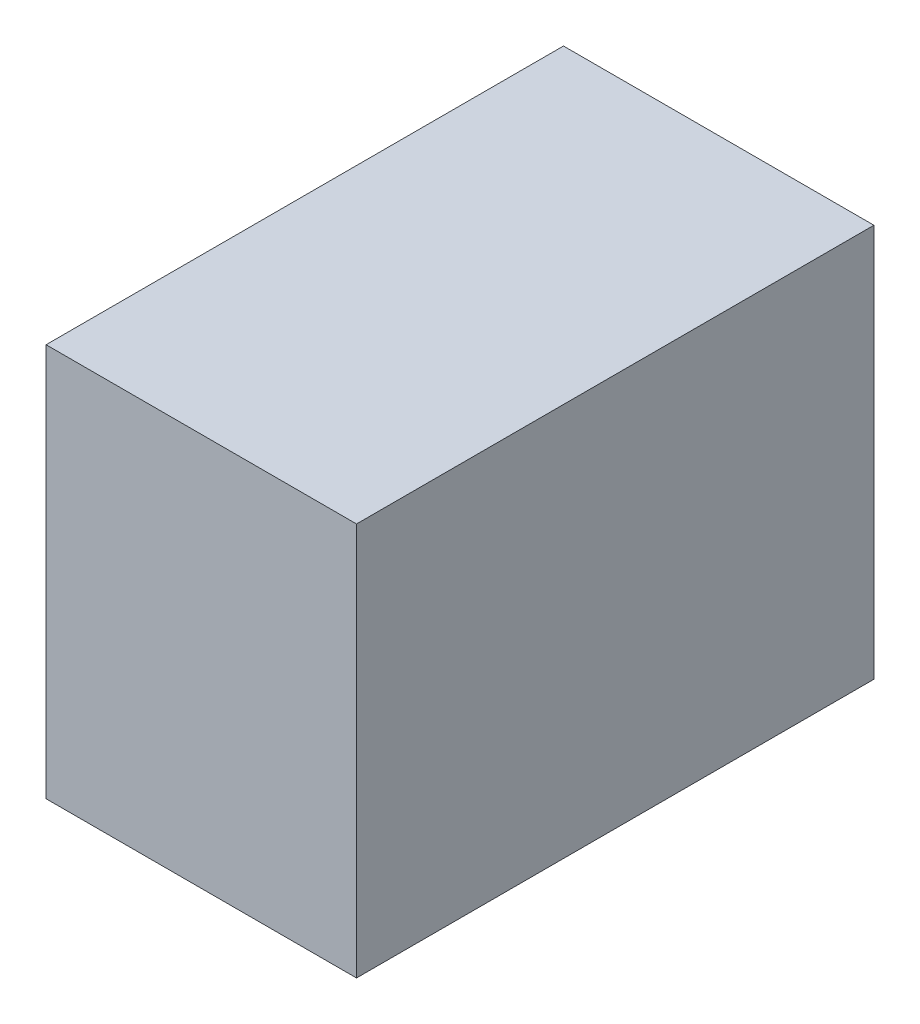
SolidWorks part; units mm, degrees
ref_plane "Front Plane" through (0, 0, 0) normal (0, 0, 1) x (1, 0, 0)
ref_plane "Top Plane" through (0, 0, 0) normal (0, 1, 0) x (1, 0, 0)
ref_plane "Right Plane" through (0, 0, 0) normal (1, 0, 0) x (0, 0, -1)
sketch "Sketch1" plane through (0, 0, 0) normal (0, 1, 0) x (1, 0, 0)
  line L1 (-750, -1250) -> (750, -1250)
  line L2 (-750, -1250) -> (-750, 1250)
  line L3 (-750, 1250) -> (750, 1250)
  line L4 (750, -1250) -> (750, 1250)
  line L5 (-750, -1250) -> (750, 1250) construction
  line L6 (-750, 1250) -> (750, -1250) construction
  point P0 (0, 0)
  dimension "D1" = 2500
  dimension "D2" = 1500
extrude "Boss-Extrude1" add sketch "Sketch1" along normal blind 1900
